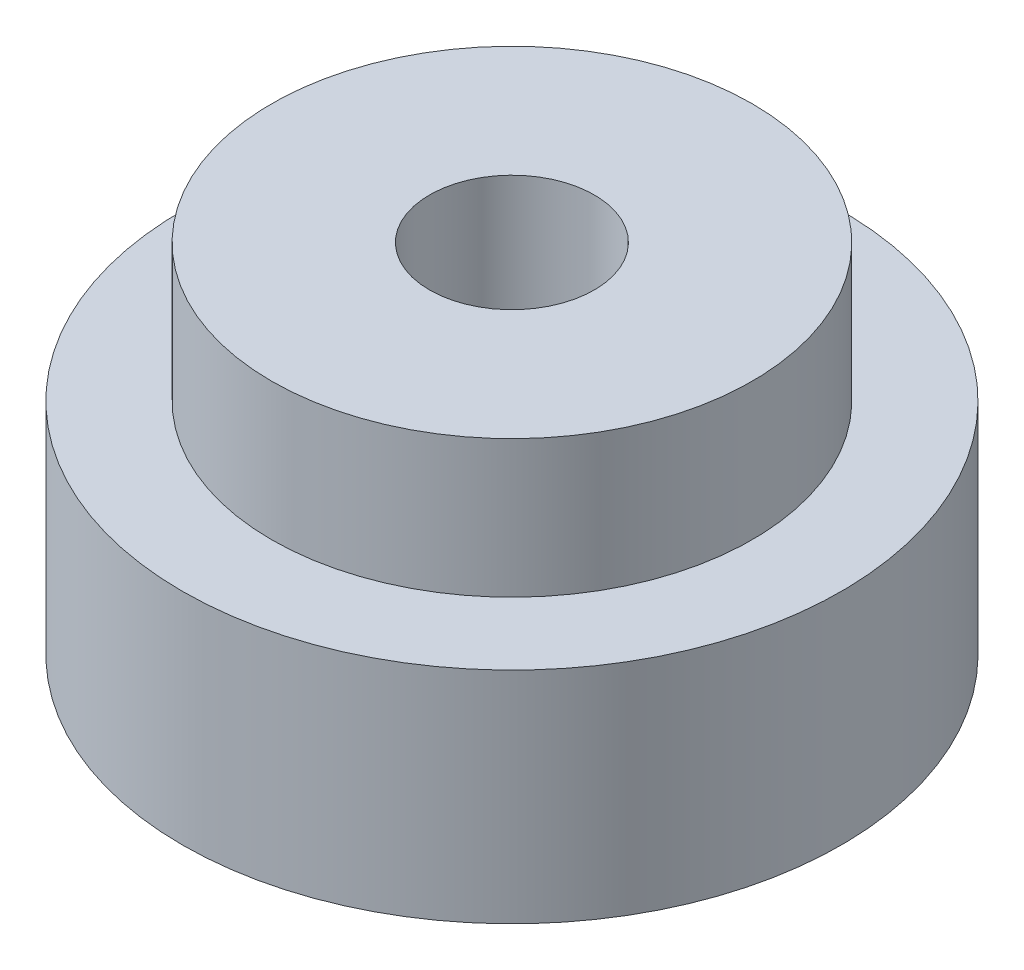
SolidWorks part; units mm, degrees
ref_plane "Front Plane" through (0, 0, 0) normal (0, 0, 1) x (1, 0, 0)
ref_plane "Top Plane" through (0, 0, 0) normal (0, 1, 0) x (1, 0, 0)
ref_plane "Right Plane" through (0, 0, 0) normal (1, 0, 0) x (0, 0, -1)
sketch "Sketch1" plane through (0, 0, 0) normal (0, 1, 0) x (1, 0, 0)
  circle A0 centre (0, 0) radius 24
  dimension "D1" = 48
extrude "Boss-Extrude1" add sketch "Sketch1" along normal blind 16
sketch "Sketch2" plane through (0, 16, 0) normal (0, 1, 0) x (1, 0, 0)
  circle A0 centre (0, 0) radius 17.5
  dimension "D1" = 35
extrude "Boss-Extrude2" add sketch "Sketch2" along normal blind 10
sketch "Sketch3" plane through (0, 26, 0) normal (0, 1, 0) x (1, 0, 0)
  circle A0 centre (0, 0) radius 6
  dimension "D1" = 12
extrude "Cut-Extrude1" cut sketch "Sketch3" against normal blind 26
